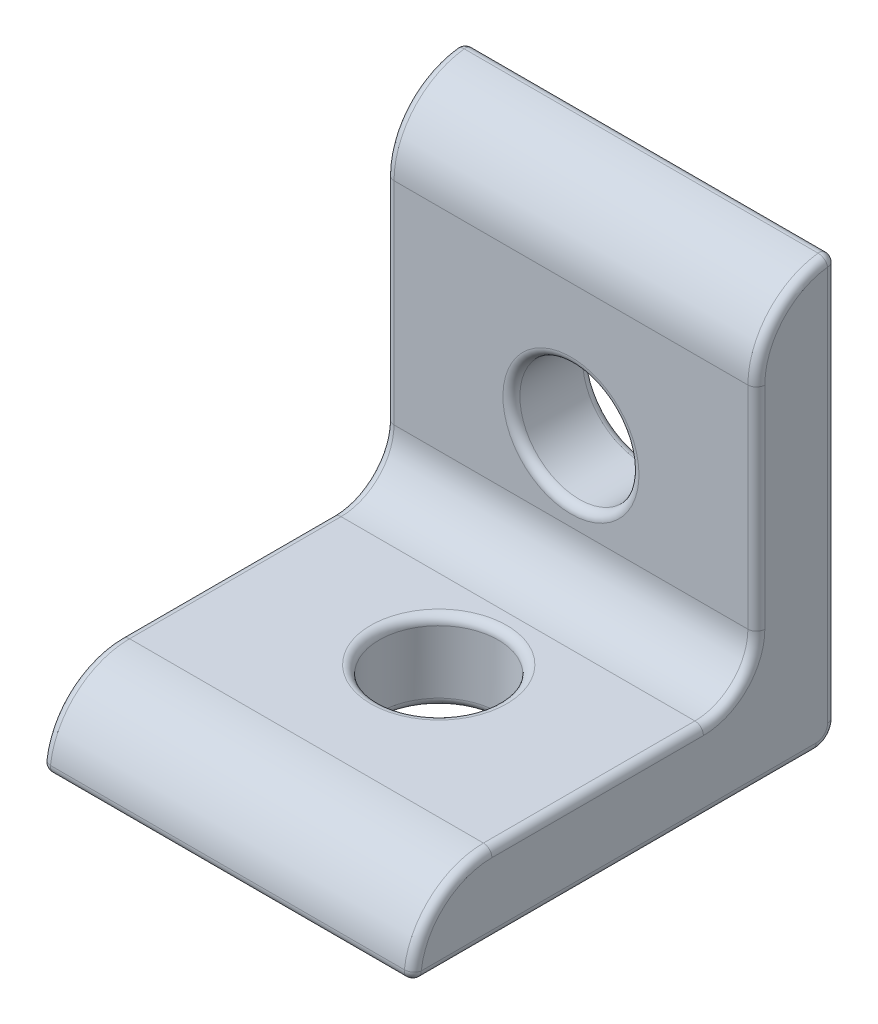
SolidWorks part; units mm, degrees
ref_plane "Front Plane" through (0, 0, 0) normal (0, 0, 1) x (1, 0, 0)
ref_plane "Top Plane" through (0, 0, 0) normal (0, 1, 0) x (1, 0, 0)
ref_plane "Right Plane" through (0, 0, 0) normal (1, 0, 0) x (0, 0, -1)
sketch "Sketch1" plane through (0, 0, 0) normal (0, 0, 1) x (1, 0, 0)
  line L0 (-11.1125, -12.7) -> (11.1125, -12.7) construction
  line L1 (0, -12.7) -> (0, 12.7) construction
  line L2 (-11.1125, 12.7) -> (11.1125, 12.7) construction
  dimension "Width" = 22.225
  dimension "Length" = 25.4
sketch "Sketch2" plane through (0, 0, 0) normal (1, 0, 0) x (0, 0, -1)
  line L0 (-20.6248, -12.7) -> (4.7752, -12.7) construction
  line L1 (0, -12.7) -> (0, 12.7) construction
  line L2 (4.7752, -12.7) -> (4.7752, 12.7) construction
  line L3 (0, 7.9248) -> (0, -4.7498)
  line L4 (-3.175, -7.9248) -> (-15.8496, -7.9248)
  line L5 (4.7752, 0) -> (0, 0) construction
  line L6 (-7.9248, -12.7) -> (-7.9248, -7.9248) construction
  line L7 (4.7752, 3.5687) -> (4.7752, -3.5687)
  line L8 (-11.4935, -12.7) -> (-4.3561, -12.7)
  line L9 (4.7752, 0) -> (12.7, 0) construction
  line L10 (12.7, 3.175) -> (12.7, -3.175) construction
  line L11 (12.7, 3.175) -> (13.97, 3.175) construction
  arc A0 (4.7752, 12.7) -> (0, 7.9248) centre (4.7752, 7.9248) ccw
  arc A1 (0, -4.7498) -> (-3.175, -7.9248) centre (-3.175, -4.7498) cw
  arc A2 (-15.8496, -7.9248) -> (-20.6248, -12.7) centre (-15.8496, -12.7) ccw
  dimension "Bracket End Radius" = 4.7752
  dimension "Bracket Corner Radius" = 3.175
  dimension "D1" = 25.4
  dimension "Bracket Thickness" = 4.7752
  dimension "Mounting Hole Diameter" = 7.1374
  dimension "Mounting Hole Offset" = 12.7
  dimension "D3" = 12.7
  dimension "Mounting Fastener Thread Length" = 12.7
  dimension "Mounting Fastener Thread Size" = 6.35
  dimension "Mounting Fastener Thread Pitch" = 1.27
sketch "Sketch3" plane through (0, 0, 0) normal (1, 0, 0) x (0, 0, -1)
  line L0 (-3.175, -7.9248) -> (-15.8496, -7.9248) construction
  line L1 (0, 7.9248) -> (0, -4.7498) construction
  line L2 (-3.175, -7.9248) -> (-15.8496, -7.9248)
  line L3 (0, 7.9248) -> (0, -4.7498)
  line L4 (-20.6248, -12.7) -> (4.7752, -12.7)
  line L5 (4.7752, -12.7) -> (4.7752, 12.7)
  arc A0 (-15.8496, -7.9248) -> (-20.6248, -12.7) centre (-15.8496, -12.7) ccw construction
  arc A1 (-3.175, -7.9248) -> (0, -4.7498) centre (-3.175, -4.7498) ccw construction
  arc A2 (4.7752, 12.7) -> (0, 7.9248) centre (4.7752, 7.9248) ccw construction
  arc A3 (-15.8496, -7.9248) -> (-20.6248, -12.7) centre (-15.8496, -12.7) ccw
  arc A4 (-3.175, -7.9248) -> (0, -4.7498) centre (-3.175, -4.7498) ccw
  arc A5 (4.7752, 12.7) -> (0, 7.9248) centre (4.7752, 7.9248) ccw
extrude "Boss-Extrude1" add sketch "Sketch3" against normal up to vertex (11.1125 mm away) from vertex at 11.1125 starting at point (11.1125, -12.7, 0)
fillet "Fillet1" radius 1.1938 1 edges at (0, -12.7, -4.7752)
sketch "Sketch4" plane through (0, 0, 0) normal (0, 0, 1) x (1, 0, 0)
  circle A0 centre (0, 0) radius 3.5687
extrude "Cut-Extrude1" cut sketch "Sketch4" against normal through all
sketch "Sketch5" plane through (0, -7.9248, 0) normal (0, 1, 0) x (1, 0, 0)
  circle A0 centre (0, -7.9248) radius 3.5687
extrude "Cut-Extrude2" cut sketch "Sketch5" against normal through all
fillet "Fillet2" radius 0.508 19 edges at (-11.1125, -12.7, 8.5217) (-11.1125, -12.3503, -4.4255) (11.1125, -12.7, 8.5217) (11.1125, -12.3503, -4.4255) (-11.1125, -9.3234, 19.2262) (-11.1125, -7.9248, 9.5123) (-11.1125, -6.9949, 0.9299) (-11.1125, 1.5875, 0) (11.1125, -9.3234, 19.2262) (11.1125, -7.9248, 9.5123) (11.1125, -6.9949, 0.9299) (11.1125, 1.5875, 0) (0, -12.7, 20.6248) (0, 12.7, -4.7752) (-11.1125, 0.5969, -4.7752) (11.1125, 0.5969, -4.7752) (-11.1125, 11.3014, -1.3986) (11.1125, 11.3014, -1.3986) (0, -12.7, 11.4935)
fillet "Fillet3" radius 0.508 3 edges at (0, -7.9248, 11.4935) (3.5687, 0, 0) (3.5687, 0, -4.7752)
ref_plane "Plane1" through (0, 0, 0) normal (1, 0, 0) x (0, 0, -1)
equation "\"D3@Sketch2\" = \"Mounting Hole Offset@Sketch2\""
equation "\"D1@Fillet1\"=\"Bracket End Radius@Sketch2\"/4"
equation "\"Bracket End Radius@Sketch2\"=\"Bracket Thickness@Sketch2\""
equation "\"D1@Sketch2\"=\"Length@Sketch1\""
